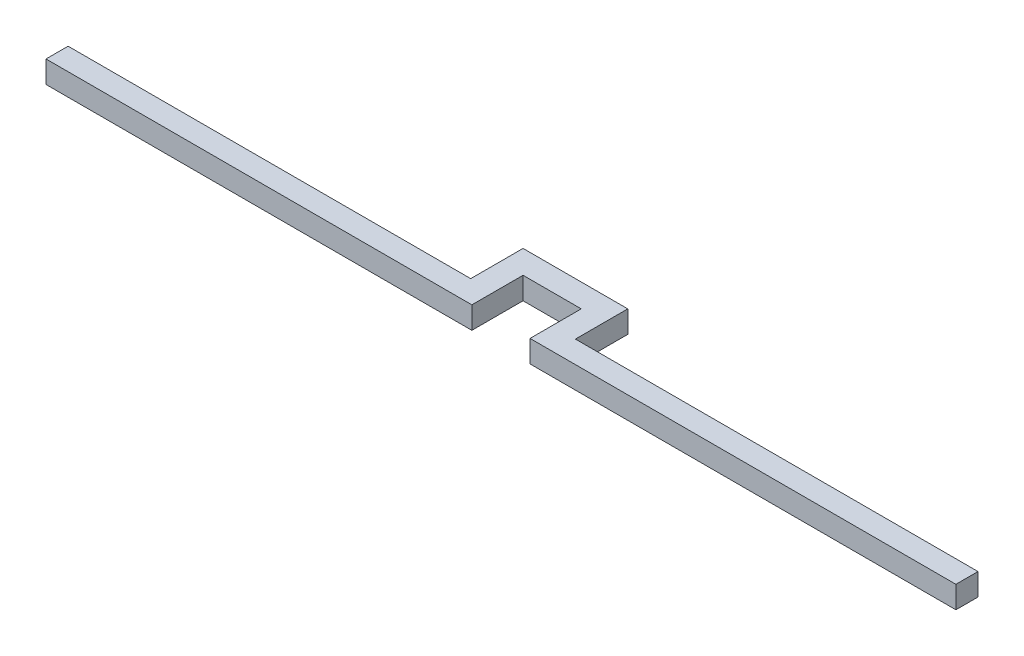
SolidWorks part; units mm, degrees
ref_plane "Front Plane" through (0, 0, 0) normal (0, 0, 1) x (1, 0, 0)
ref_plane "Top Plane" through (0, 0, 0) normal (0, 1, 0) x (1, 0, 0)
ref_plane "Right Plane" through (0, 0, 0) normal (1, 0, 0) x (0, 0, -1)
sketch "Sketch1" plane through (0, 0, 0) normal (0, 1, 0) x (1, 0, 0)
  line L0 (2.5, 3.5) -> (-2.5, 3.5)
  line L1 (-39.1, 1) -> (-4.5, 1)
  line L2 (-39.1, 1) -> (-39.1, -0.9)
  line L3 (-39.1, -0.9) -> (-2.5, -0.9)
  line L4 (39.1, 1) -> (39.1, -0.9)
  line L8 (-2.5, 1) -> (-2.5, 3.5)
  line L10 (-4.5, 1) -> (-4.5, 3.5)
  line L12 (2.5, 1) -> (2.5, 3.5)
  line L14 (4.5, 1) -> (4.5, 3.5)
  line L15 (4.5, 3.5) -> (4.5, 5.5)
  line L16 (-4.5, 3.5) -> (-4.5, 5.5)
  line L17 (4.5, 5.5) -> (-4.5, 5.5)
  line L18 (-2.5, 1) -> (-2.5, -0.9)
  line L19 (2.5, 1) -> (2.5, -0.9)
  line L20 (4.5, 1) -> (39.1, 1)
  line L21 (2.5, -0.9) -> (39.1, -0.9)
  point P0 (0, 0)
  dimension "D1" = 78.2
  dimension "D2" = 1.9
  dimension "D3" = 2
  dimension "D4" = 2.5
  dimension "D5" = 2.5
  dimension "D6" = 2.5
  dimension "D7" = 2.5
  dimension "D8" = 2
  dimension "D9" = 2
extrude "Boss-Extrude1" add sketch "Sketch1" along normal blind 1.9
